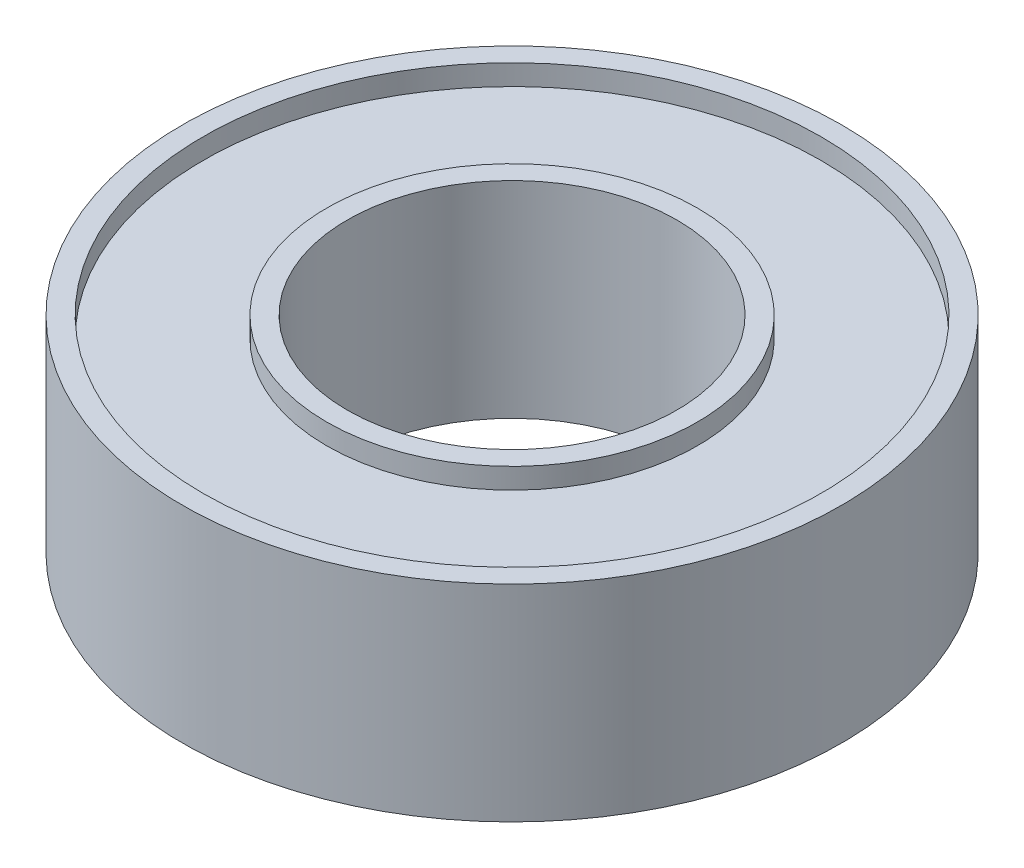
SolidWorks part; units mm, degrees
ref_plane "Front Plane" through (0, 0, 0) normal (0, 0, 1) x (1, 0, 0)
ref_plane "Top Plane" through (0, 0, 0) normal (0, 1, 0) x (1, 0, 0)
ref_plane "Right Plane" through (0, 0, 0) normal (1, 0, 0) x (0, 0, -1)
sketch "Sketch1" plane through (0, 0, 0) normal (0, 0, 1) x (1, 0, 0)
  line L0 (-4, 4.5) -> (-4.5, 4.5)
  line L1 (-4.5, 4.5) -> (-4.5, 4)
  line L2 (-4.5, 4) -> (-7.5, 4)
  line L3 (-7.5, 4) -> (-7.5, 4.5)
  line L4 (-7.5, 4.5) -> (-8, 4.5)
  line L5 (-8, 4.5) -> (-8, -0.5)
  line L6 (-8, -0.5) -> (-7.5, -0.5)
  line L7 (-7.5, -0.5) -> (-7.5, 0)
  line L8 (-7.5, 0) -> (-4.5, 0)
  line L9 (-4.5, 0) -> (-4.5, -0.5)
  line L10 (-4.5, -0.5) -> (-4, -0.5)
  line L11 (0, 0) -> (0, 9.4844) construction
  line L12 (-4, -0.5) -> (-4, 4.5)
  dimension "D1" = 8
  dimension "D2" = 4
  dimension "D3" = 0.5
  dimension "D5" = 5
revolve "Revolve1" add sketch "Sketch1" angle 360 about L11
equation "\"D_hull\"= 8"
equation "\"D\"= 16"
equation "\"tykkelse\"= 5"
equation "\"D2@Sketch1\"=\"D_hull\"/2"
equation "\"D1@Sketch1\"=\"D\"/2"
equation "\"D5@Sketch1\"=\"tykkelse\""
equation "\"D3@Sketch1\"=0.5"
